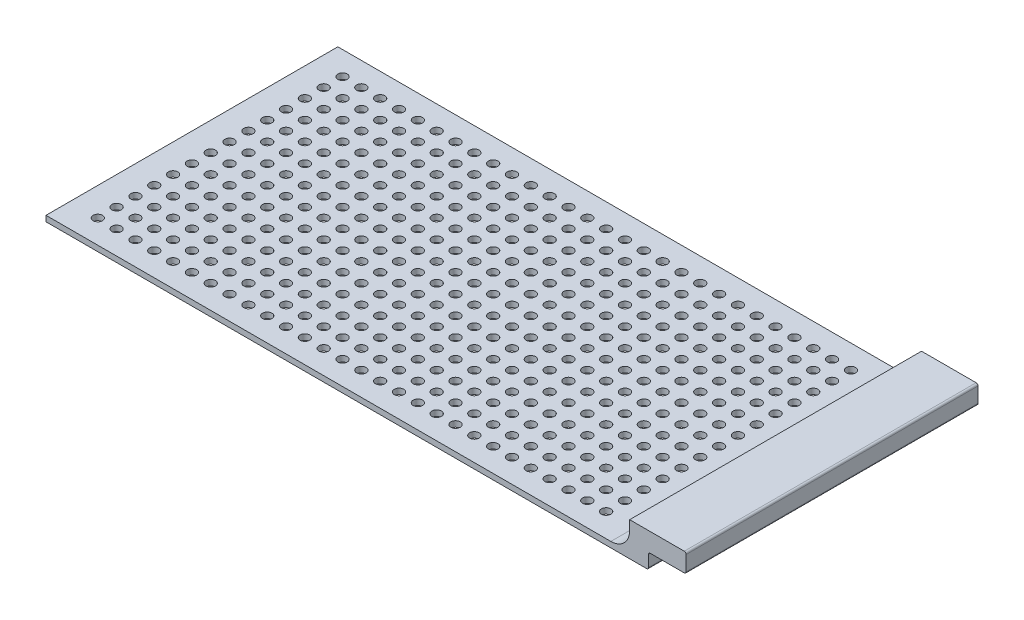
SolidWorks part; units mm, degrees
ref_plane "Front Plane" through (0, 0, 0) normal (0, 0, 1) x (1, 0, 0)
ref_plane "Top Plane" through (0, 0, 0) normal (0, 1, 0) x (1, 0, 0)
ref_plane "Right Plane" through (0, 0, 0) normal (1, 0, 0) x (0, 0, -1)
sketch "Sketch1" plane through (0, 0, 0) normal (0, 0, 1) x (1, 0, 0)
  line L1 (0, 0) -> (310, 0)
  line L2 (0, 0) -> (0, 3)
  line L3 (0, 3) -> (310, 3)
  line L4 (310, 0) -> (310, 3)
  dimension "D1" = 3
  dimension "D2" = 310
extrude "Mesh Block" add sketch "Sketch1" along normal blind 155
sketch "Sketch2" plane through (0, 3, 0) normal (0, 1, 0) x (1, 0, 0)
  line L0 (0, -142.5) -> (15, -142.5) construction
  line L1 (0, -155) -> (0, 0) construction
  line L2 (310, -155) -> (0, -155) construction
  line L3 (15, -155) -> (15, 0) construction
  line L4 (310, 0) -> (0, 0) construction
  line L5 (295, -155) -> (295, 0) construction
  line L6 (310, -155) -> (310, 0) construction
  line L7 (15, -142.5) -> (25, -142.5) construction
  line L8 (15, -142.5) -> (15, -132.5) construction
  line L9 (15, -52.5) -> (15, -42.5) construction
  line L10 (185, -142.5) -> (195, -142.5) construction
  circle A0 centre (15, -142.5) radius 2.5
  circle A1 centre (25, -142.5) radius 2.5
  circle A2 centre (35, -142.5) radius 2.5
  circle A3 centre (45, -142.5) radius 2.5
  circle A4 centre (55, -142.5) radius 2.5
  circle A5 centre (65, -142.5) radius 2.5
  circle A6 centre (75, -142.5) radius 2.5
  circle A7 centre (85, -142.5) radius 2.5
  circle A8 centre (95, -142.5) radius 2.5
  circle A9 centre (105, -142.5) radius 2.5
  circle A10 centre (115, -142.5) radius 2.5
  circle A11 centre (125, -142.5) radius 2.5
  circle A12 centre (135, -142.5) radius 2.5
  circle A13 centre (145, -142.5) radius 2.5
  circle A14 centre (155, -142.5) radius 2.5
  circle A15 centre (165, -142.5) radius 2.5
  circle A16 centre (175, -142.5) radius 2.5
  circle A17 centre (185, -142.5) radius 2.5
  circle A18 centre (15, -132.5) radius 2.5
  circle A19 centre (185, -132.5) radius 2.5
  circle A20 centre (175, -132.5) radius 2.5
  circle A21 centre (165, -132.5) radius 2.5
  circle A22 centre (155, -132.5) radius 2.5
  circle A23 centre (145, -132.5) radius 2.5
  circle A24 centre (135, -132.5) radius 2.5
  circle A25 centre (125, -132.5) radius 2.5
  circle A26 centre (115, -132.5) radius 2.5
  circle A27 centre (105, -132.5) radius 2.5
  circle A28 centre (25, -132.5) radius 2.5
  circle A29 centre (35, -132.5) radius 2.5
  circle A30 centre (45, -132.5) radius 2.5
  circle A31 centre (55, -132.5) radius 2.5
  circle A32 centre (65, -132.5) radius 2.5
  circle A33 centre (75, -132.5) radius 2.5
  circle A34 centre (85, -132.5) radius 2.5
  circle A35 centre (95, -132.5) radius 2.5
  circle A36 centre (15, -122.5) radius 2.5
  circle A37 centre (185, -122.5) radius 2.5
  circle A38 centre (175, -122.5) radius 2.5
  circle A39 centre (165, -122.5) radius 2.5
  circle A40 centre (155, -122.5) radius 2.5
  circle A41 centre (145, -122.5) radius 2.5
  circle A42 centre (135, -122.5) radius 2.5
  circle A43 centre (125, -122.5) radius 2.5
  circle A44 centre (115, -122.5) radius 2.5
  circle A45 centre (105, -122.5) radius 2.5
  circle A46 centre (25, -122.5) radius 2.5
  circle A47 centre (35, -122.5) radius 2.5
  circle A48 centre (45, -122.5) radius 2.5
  circle A49 centre (55, -122.5) radius 2.5
  circle A50 centre (65, -122.5) radius 2.5
  circle A51 centre (75, -122.5) radius 2.5
  circle A52 centre (85, -122.5) radius 2.5
  circle A53 centre (95, -122.5) radius 2.5
  circle A54 centre (15, -112.5) radius 2.5
  circle A55 centre (185, -112.5) radius 2.5
  circle A56 centre (175, -112.5) radius 2.5
  circle A57 centre (165, -112.5) radius 2.5
  circle A58 centre (155, -112.5) radius 2.5
  circle A59 centre (145, -112.5) radius 2.5
  circle A60 centre (135, -112.5) radius 2.5
  circle A61 centre (125, -112.5) radius 2.5
  circle A62 centre (115, -112.5) radius 2.5
  circle A63 centre (105, -112.5) radius 2.5
  circle A64 centre (25, -112.5) radius 2.5
  circle A65 centre (35, -112.5) radius 2.5
  circle A66 centre (45, -112.5) radius 2.5
  circle A67 centre (55, -112.5) radius 2.5
  circle A68 centre (65, -112.5) radius 2.5
  circle A69 centre (75, -112.5) radius 2.5
  circle A70 centre (85, -112.5) radius 2.5
  circle A71 centre (95, -112.5) radius 2.5
  circle A72 centre (15, -102.5) radius 2.5
  circle A73 centre (185, -102.5) radius 2.5
  circle A74 centre (175, -102.5) radius 2.5
  circle A75 centre (165, -102.5) radius 2.5
  circle A76 centre (155, -102.5) radius 2.5
  circle A77 centre (145, -102.5) radius 2.5
  circle A78 centre (135, -102.5) radius 2.5
  circle A79 centre (125, -102.5) radius 2.5
  circle A80 centre (115, -102.5) radius 2.5
  circle A81 centre (105, -102.5) radius 2.5
  circle A82 centre (25, -102.5) radius 2.5
  circle A83 centre (35, -102.5) radius 2.5
  circle A84 centre (45, -102.5) radius 2.5
  circle A85 centre (55, -102.5) radius 2.5
  circle A86 centre (65, -102.5) radius 2.5
  circle A87 centre (75, -102.5) radius 2.5
  circle A88 centre (85, -102.5) radius 2.5
  circle A89 centre (95, -102.5) radius 2.5
  circle A90 centre (15, -92.5) radius 2.5
  circle A91 centre (185, -92.5) radius 2.5
  circle A92 centre (175, -92.5) radius 2.5
  circle A93 centre (165, -92.5) radius 2.5
  circle A94 centre (155, -92.5) radius 2.5
  circle A95 centre (145, -92.5) radius 2.5
  circle A96 centre (135, -92.5) radius 2.5
  circle A97 centre (125, -92.5) radius 2.5
  circle A98 centre (115, -92.5) radius 2.5
  circle A99 centre (105, -92.5) radius 2.5
  circle A100 centre (25, -92.5) radius 2.5
  circle A101 centre (35, -92.5) radius 2.5
  circle A102 centre (45, -92.5) radius 2.5
  circle A103 centre (55, -92.5) radius 2.5
  circle A104 centre (65, -92.5) radius 2.5
  circle A105 centre (75, -92.5) radius 2.5
  circle A106 centre (85, -92.5) radius 2.5
  circle A107 centre (95, -92.5) radius 2.5
  circle A108 centre (15, -82.5) radius 2.5
  circle A109 centre (185, -82.5) radius 2.5
  circle A110 centre (175, -82.5) radius 2.5
  circle A111 centre (165, -82.5) radius 2.5
  circle A112 centre (155, -82.5) radius 2.5
  circle A113 centre (145, -82.5) radius 2.5
  circle A114 centre (135, -82.5) radius 2.5
  circle A115 centre (125, -82.5) radius 2.5
  circle A116 centre (115, -82.5) radius 2.5
  circle A117 centre (105, -82.5) radius 2.5
  circle A118 centre (25, -82.5) radius 2.5
  circle A119 centre (35, -82.5) radius 2.5
  circle A120 centre (45, -82.5) radius 2.5
  circle A121 centre (55, -82.5) radius 2.5
  circle A122 centre (65, -82.5) radius 2.5
  circle A123 centre (75, -82.5) radius 2.5
  circle A124 centre (85, -82.5) radius 2.5
  circle A125 centre (95, -82.5) radius 2.5
  circle A126 centre (15, -72.5) radius 2.5
  circle A127 centre (185, -72.5) radius 2.5
  circle A128 centre (175, -72.5) radius 2.5
  circle A129 centre (165, -72.5) radius 2.5
  circle A130 centre (155, -72.5) radius 2.5
  circle A131 centre (145, -72.5) radius 2.5
  circle A132 centre (135, -72.5) radius 2.5
  circle A133 centre (125, -72.5) radius 2.5
  circle A134 centre (115, -72.5) radius 2.5
  circle A135 centre (105, -72.5) radius 2.5
  circle A136 centre (25, -72.5) radius 2.5
  circle A137 centre (35, -72.5) radius 2.5
  circle A138 centre (45, -72.5) radius 2.5
  circle A139 centre (55, -72.5) radius 2.5
  circle A140 centre (65, -72.5) radius 2.5
  circle A141 centre (75, -72.5) radius 2.5
  circle A142 centre (85, -72.5) radius 2.5
  circle A143 centre (95, -72.5) radius 2.5
  circle A144 centre (15, -62.5) radius 2.5
  circle A145 centre (185, -62.5) radius 2.5
  circle A146 centre (175, -62.5) radius 2.5
  circle A147 centre (165, -62.5) radius 2.5
  circle A148 centre (155, -62.5) radius 2.5
  circle A149 centre (145, -62.5) radius 2.5
  circle A150 centre (135, -62.5) radius 2.5
  circle A151 centre (125, -62.5) radius 2.5
  circle A152 centre (115, -62.5) radius 2.5
  circle A153 centre (105, -62.5) radius 2.5
  circle A154 centre (25, -62.5) radius 2.5
  circle A155 centre (35, -62.5) radius 2.5
  circle A156 centre (45, -62.5) radius 2.5
  circle A157 centre (55, -62.5) radius 2.5
  circle A158 centre (65, -62.5) radius 2.5
  circle A159 centre (75, -62.5) radius 2.5
  circle A160 centre (85, -62.5) radius 2.5
  circle A161 centre (95, -62.5) radius 2.5
  circle A162 centre (15, -52.5) radius 2.5
  circle A163 centre (185, -52.5) radius 2.5
  circle A164 centre (175, -52.5) radius 2.5
  circle A165 centre (165, -52.5) radius 2.5
  circle A166 centre (155, -52.5) radius 2.5
  circle A167 centre (145, -52.5) radius 2.5
  circle A168 centre (135, -52.5) radius 2.5
  circle A169 centre (125, -52.5) radius 2.5
  circle A170 centre (115, -52.5) radius 2.5
  circle A171 centre (105, -52.5) radius 2.5
  circle A172 centre (25, -52.5) radius 2.5
  circle A173 centre (35, -52.5) radius 2.5
  circle A174 centre (45, -52.5) radius 2.5
  circle A175 centre (55, -52.5) radius 2.5
  circle A176 centre (65, -52.5) radius 2.5
  circle A177 centre (75, -52.5) radius 2.5
  circle A178 centre (85, -52.5) radius 2.5
  circle A179 centre (95, -52.5) radius 2.5
  circle A180 centre (15, -42.5) radius 2.5
  circle A181 centre (25, -42.5) radius 2.5
  circle A182 centre (35, -42.5) radius 2.5
  circle A183 centre (45, -42.5) radius 2.5
  circle A184 centre (55, -42.5) radius 2.5
  circle A185 centre (65, -42.5) radius 2.5
  circle A186 centre (75, -42.5) radius 2.5
  circle A187 centre (85, -42.5) radius 2.5
  circle A188 centre (95, -42.5) radius 2.5
  circle A189 centre (105, -42.5) radius 2.5
  circle A190 centre (115, -42.5) radius 2.5
  circle A191 centre (125, -42.5) radius 2.5
  circle A192 centre (135, -42.5) radius 2.5
  circle A193 centre (145, -42.5) radius 2.5
  circle A194 centre (155, -42.5) radius 2.5
  circle A195 centre (165, -42.5) radius 2.5
  circle A196 centre (175, -42.5) radius 2.5
  circle A197 centre (185, -42.5) radius 2.5
  circle A198 centre (15, -32.5) radius 2.5
  circle A199 centre (25, -32.5) radius 2.5
  circle A200 centre (35, -32.5) radius 2.5
  circle A201 centre (45, -32.5) radius 2.5
  circle A202 centre (55, -32.5) radius 2.5
  circle A203 centre (65, -32.5) radius 2.5
  circle A204 centre (75, -32.5) radius 2.5
  circle A205 centre (85, -32.5) radius 2.5
  circle A206 centre (95, -32.5) radius 2.5
  circle A207 centre (105, -32.5) radius 2.5
  circle A208 centre (115, -32.5) radius 2.5
  circle A209 centre (125, -32.5) radius 2.5
  circle A210 centre (135, -32.5) radius 2.5
  circle A211 centre (145, -32.5) radius 2.5
  circle A212 centre (155, -32.5) radius 2.5
  circle A213 centre (165, -32.5) radius 2.5
  circle A214 centre (175, -32.5) radius 2.5
  circle A215 centre (185, -32.5) radius 2.5
  circle A216 centre (15, -22.5) radius 2.5
  circle A217 centre (25, -22.5) radius 2.5
  circle A218 centre (35, -22.5) radius 2.5
  circle A219 centre (45, -22.5) radius 2.5
  circle A220 centre (55, -22.5) radius 2.5
  circle A221 centre (65, -22.5) radius 2.5
  circle A222 centre (75, -22.5) radius 2.5
  circle A223 centre (85, -22.5) radius 2.5
  circle A224 centre (95, -22.5) radius 2.5
  circle A225 centre (105, -22.5) radius 2.5
  circle A226 centre (115, -22.5) radius 2.5
  circle A227 centre (125, -22.5) radius 2.5
  circle A228 centre (135, -22.5) radius 2.5
  circle A229 centre (145, -22.5) radius 2.5
  circle A230 centre (155, -22.5) radius 2.5
  circle A231 centre (165, -22.5) radius 2.5
  circle A232 centre (175, -22.5) radius 2.5
  circle A233 centre (185, -22.5) radius 2.5
  circle A234 centre (15, -12.5) radius 2.5
  circle A235 centre (25, -12.5) radius 2.5
  circle A236 centre (35, -12.5) radius 2.5
  circle A237 centre (45, -12.5) radius 2.5
  circle A238 centre (55, -12.5) radius 2.5
  circle A239 centre (65, -12.5) radius 2.5
  circle A240 centre (75, -12.5) radius 2.5
  circle A241 centre (85, -12.5) radius 2.5
  circle A242 centre (95, -12.5) radius 2.5
  circle A243 centre (105, -12.5) radius 2.5
  circle A244 centre (115, -12.5) radius 2.5
  circle A245 centre (125, -12.5) radius 2.5
  circle A246 centre (135, -12.5) radius 2.5
  circle A247 centre (145, -12.5) radius 2.5
  circle A248 centre (155, -12.5) radius 2.5
  circle A249 centre (165, -12.5) radius 2.5
  circle A250 centre (175, -12.5) radius 2.5
  circle A251 centre (185, -12.5) radius 2.5
  circle A270 centre (195, -142.5) radius 2.5
  circle A271 centre (195, -132.5) radius 2.5
  circle A272 centre (195, -122.5) radius 2.5
  circle A273 centre (195, -102.5) radius 2.5
  circle A274 centre (195, -112.5) radius 2.5
  circle A275 centre (195, -92.5) radius 2.5
  circle A276 centre (195, -82.5) radius 2.5
  circle A277 centre (195, -72.5) radius 2.5
  circle A278 centre (195, -62.5) radius 2.5
  circle A279 centre (195, -52.5) radius 2.5
  circle A280 centre (195, -42.5) radius 2.5
  circle A281 centre (195, -32.5) radius 2.5
  circle A282 centre (195, -22.5) radius 2.5
  circle A283 centre (195, -12.5) radius 2.5
  circle A285 centre (205, -142.5) radius 2.5
  circle A286 centre (205, -132.5) radius 2.5
  circle A287 centre (205, -122.5) radius 2.5
  circle A288 centre (205, -102.5) radius 2.5
  circle A289 centre (205, -112.5) radius 2.5
  circle A290 centre (205, -92.5) radius 2.5
  circle A291 centre (205, -82.5) radius 2.5
  circle A292 centre (205, -72.5) radius 2.5
  circle A293 centre (205, -62.5) radius 2.5
  circle A294 centre (205, -52.5) radius 2.5
  circle A295 centre (205, -42.5) radius 2.5
  circle A296 centre (205, -32.5) radius 2.5
  circle A297 centre (205, -22.5) radius 2.5
  circle A298 centre (205, -12.5) radius 2.5
  circle A300 centre (215, -142.5) radius 2.5
  circle A301 centre (215, -132.5) radius 2.5
  circle A302 centre (215, -122.5) radius 2.5
  circle A303 centre (215, -102.5) radius 2.5
  circle A304 centre (215, -112.5) radius 2.5
  circle A305 centre (215, -92.5) radius 2.5
  circle A306 centre (215, -82.5) radius 2.5
  circle A307 centre (215, -72.5) radius 2.5
  circle A308 centre (215, -62.5) radius 2.5
  circle A309 centre (215, -52.5) radius 2.5
  circle A310 centre (215, -42.5) radius 2.5
  circle A311 centre (215, -32.5) radius 2.5
  circle A312 centre (215, -22.5) radius 2.5
  circle A313 centre (215, -12.5) radius 2.5
  circle A315 centre (225, -142.5) radius 2.5
  circle A316 centre (225, -132.5) radius 2.5
  circle A317 centre (225, -122.5) radius 2.5
  circle A318 centre (225, -102.5) radius 2.5
  circle A319 centre (225, -112.5) radius 2.5
  circle A320 centre (225, -92.5) radius 2.5
  circle A321 centre (225, -82.5) radius 2.5
  circle A322 centre (225, -72.5) radius 2.5
  circle A323 centre (225, -62.5) radius 2.5
  circle A324 centre (225, -52.5) radius 2.5
  circle A325 centre (225, -42.5) radius 2.5
  circle A326 centre (225, -32.5) radius 2.5
  circle A327 centre (225, -22.5) radius 2.5
  circle A328 centre (225, -12.5) radius 2.5
  circle A330 centre (235, -142.5) radius 2.5
  circle A331 centre (235, -132.5) radius 2.5
  circle A332 centre (235, -122.5) radius 2.5
  circle A333 centre (235, -102.5) radius 2.5
  circle A334 centre (235, -112.5) radius 2.5
  circle A335 centre (235, -92.5) radius 2.5
  circle A336 centre (235, -82.5) radius 2.5
  circle A337 centre (235, -72.5) radius 2.5
  circle A338 centre (235, -62.5) radius 2.5
  circle A339 centre (235, -52.5) radius 2.5
  circle A340 centre (235, -42.5) radius 2.5
  circle A341 centre (235, -32.5) radius 2.5
  circle A342 centre (235, -22.5) radius 2.5
  circle A343 centre (235, -12.5) radius 2.5
  circle A345 centre (245, -142.5) radius 2.5
  circle A346 centre (245, -132.5) radius 2.5
  circle A347 centre (245, -122.5) radius 2.5
  circle A348 centre (245, -102.5) radius 2.5
  circle A349 centre (245, -112.5) radius 2.5
  circle A350 centre (245, -92.5) radius 2.5
  circle A351 centre (245, -82.5) radius 2.5
  circle A352 centre (245, -72.5) radius 2.5
  circle A353 centre (245, -62.5) radius 2.5
  circle A354 centre (245, -52.5) radius 2.5
  circle A355 centre (245, -42.5) radius 2.5
  circle A356 centre (245, -32.5) radius 2.5
  circle A357 centre (245, -22.5) radius 2.5
  circle A358 centre (245, -12.5) radius 2.5
  circle A360 centre (255, -142.5) radius 2.5
  circle A361 centre (255, -132.5) radius 2.5
  circle A362 centre (255, -122.5) radius 2.5
  circle A363 centre (255, -102.5) radius 2.5
  circle A364 centre (255, -112.5) radius 2.5
  circle A365 centre (255, -92.5) radius 2.5
  circle A366 centre (255, -82.5) radius 2.5
  circle A367 centre (255, -72.5) radius 2.5
  circle A368 centre (255, -62.5) radius 2.5
  circle A369 centre (255, -52.5) radius 2.5
  circle A370 centre (255, -42.5) radius 2.5
  circle A371 centre (255, -32.5) radius 2.5
  circle A372 centre (255, -22.5) radius 2.5
  circle A373 centre (255, -12.5) radius 2.5
  circle A375 centre (265, -142.5) radius 2.5
  circle A376 centre (265, -132.5) radius 2.5
  circle A377 centre (265, -122.5) radius 2.5
  circle A378 centre (265, -102.5) radius 2.5
  circle A379 centre (265, -112.5) radius 2.5
  circle A380 centre (265, -92.5) radius 2.5
  circle A381 centre (265, -82.5) radius 2.5
  circle A382 centre (265, -72.5) radius 2.5
  circle A383 centre (265, -62.5) radius 2.5
  circle A384 centre (265, -52.5) radius 2.5
  circle A385 centre (265, -42.5) radius 2.5
  circle A386 centre (265, -32.5) radius 2.5
  circle A387 centre (265, -22.5) radius 2.5
  circle A388 centre (265, -12.5) radius 2.5
  circle A390 centre (275, -142.5) radius 2.5
  circle A391 centre (275, -132.5) radius 2.5
  circle A392 centre (275, -122.5) radius 2.5
  circle A393 centre (275, -102.5) radius 2.5
  circle A394 centre (275, -112.5) radius 2.5
  circle A395 centre (275, -92.5) radius 2.5
  circle A396 centre (275, -82.5) radius 2.5
  circle A397 centre (275, -72.5) radius 2.5
  circle A398 centre (275, -62.5) radius 2.5
  circle A399 centre (275, -52.5) radius 2.5
  circle A400 centre (275, -42.5) radius 2.5
  circle A401 centre (275, -32.5) radius 2.5
  circle A402 centre (275, -22.5) radius 2.5
  circle A403 centre (275, -12.5) radius 2.5
  circle A405 centre (285, -142.5) radius 2.5
  circle A406 centre (285, -132.5) radius 2.5
  circle A407 centre (285, -122.5) radius 2.5
  circle A408 centre (285, -102.5) radius 2.5
  circle A409 centre (285, -112.5) radius 2.5
  circle A410 centre (285, -92.5) radius 2.5
  circle A411 centre (285, -82.5) radius 2.5
  circle A412 centre (285, -72.5) radius 2.5
  circle A413 centre (285, -62.5) radius 2.5
  circle A414 centre (285, -52.5) radius 2.5
  circle A415 centre (285, -42.5) radius 2.5
  circle A416 centre (285, -32.5) radius 2.5
  circle A417 centre (285, -22.5) radius 2.5
  circle A418 centre (285, -12.5) radius 2.5
  circle A420 centre (15, -2.5) radius 2.5 [skipped]
  circle A421 centre (25, -2.5) radius 2.5 [skipped]
  circle A422 centre (45, -2.5) radius 2.5 [skipped]
  circle A423 centre (55, -2.5) radius 2.5 [skipped]
  circle A424 centre (35, -2.5) radius 2.5 [skipped]
  circle A425 centre (65, -2.5) radius 2.5 [skipped]
  circle A426 centre (75, -2.5) radius 2.5 [skipped]
  circle A427 centre (85, -2.5) radius 2.5 [skipped]
  circle A428 centre (95, -2.5) radius 2.5 [skipped]
  circle A429 centre (105, -2.5) radius 2.5 [skipped]
  circle A430 centre (115, -2.5) radius 2.5 [skipped]
  circle A431 centre (125, -2.5) radius 2.5 [skipped]
  circle A432 centre (135, -2.5) radius 2.5 [skipped]
  circle A433 centre (145, -2.5) radius 2.5 [skipped]
  circle A434 centre (155, -2.5) radius 2.5 [skipped]
  circle A435 centre (165, -2.5) radius 2.5 [skipped]
  circle A436 centre (175, -2.5) radius 2.5 [skipped]
  circle A437 centre (185, -2.5) radius 2.5 [skipped]
  dimension "D4" = 5
  dimension "D1" = 15
  dimension "D2" = 12.5
  dimension "D3" = 15
  dimension "D6" = 10
  dimension "D8" = 10
  dimension "D10" = 10
  dimension "D12" = 10
  dimension "D5" = 18
  dimension "D7" = 10
  dimension "D9" = 6
  dimension "D11" = 11
extrude "Mesh Holes" cut sketch "Sketch2" against normal through all
sketch "Sketch3" plane through (0, 0, 155) normal (0, 0, 1) x (1, 0, 0)
  line L0 (310, 0) -> (320, 0)
  line L1 (320, 0) -> (320, 8)
  line L2 (320, 8) -> (340, 8)
  line L3 (340, 8) -> (340, 18)
  line L4 (340, 18) -> (310, 18)
  line L5 (310, 18) -> (310, 3)
  line L6 (310, 3) -> (310, 0)
  dimension "D1" = 15
  dimension "D2" = 10
  dimension "D3" = 20
  dimension "D4" = 10
extrude "Boss-Extrude1" add sketch "Sketch3" against normal up to surface (155 mm away)
fillet "Fillet2" radius 10 1 edges at (310, 3, 77.5)
fillet "Fillet3" radius 1 4 edges at (340, 18, 77.5) (340, 8, 77.5) (320, 0, 77.5) (320, 8, 77.5)
